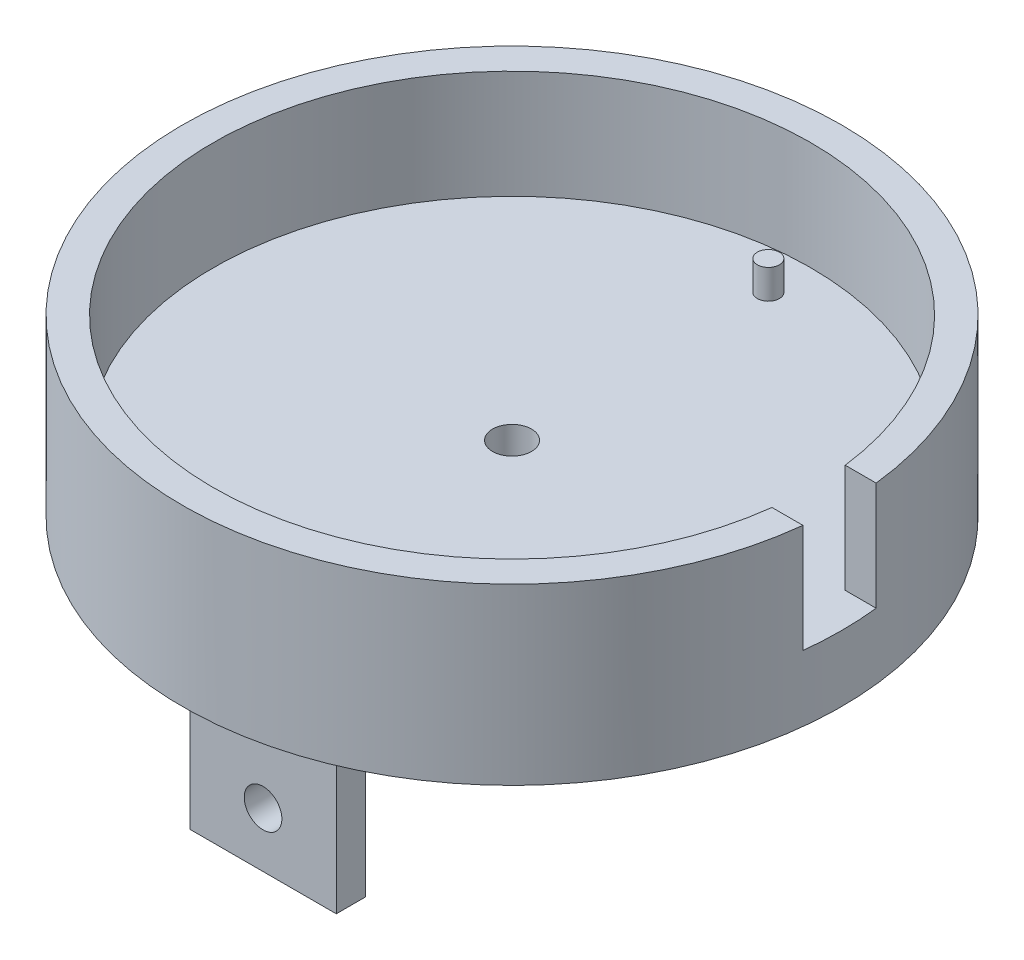
SolidWorks part; units mm, degrees
ref_plane "Front Plane" through (0, 0, 0) normal (0, 0, 1) x (1, 0, 0)
ref_plane "Top Plane" through (0, 0, 0) normal (0, 1, 0) x (1, 0, 0)
ref_plane "Right Plane" through (0, 0, 0) normal (1, 0, 0) x (0, 0, -1)
sketch "Sketch1" plane through (0, 0, 0) normal (0, 0, 1) x (1, 0, 0)
  line L0 (0, 0) -> (0, 120.0887) construction
  line L1 (0, 0) -> (57.15, 0)
  line L2 (57.15, 0) -> (57.15, 30.226)
  line L3 (57.15, 30.226) -> (51.816, 30.226)
  line L4 (51.816, 30.226) -> (51.816, 11.43)
  line L5 (51.816, 11.43) -> (0, 11.43)
  line L6 (0, 11.43) -> (0, 0)
  dimension "D1" = 51.816
  dimension "D2" = 11.43
  dimension "D3" = 5.334
  dimension "D4" = 18.796
revolve "Revolve1" add sketch "Sketch1" angle 360 mid plane about L0
ref_plane "Plane2" through (57.15, 0, 0) normal (1, 0, 0) x (0, 0, -1)
sketch "Sketch4" plane through (57.15, 0, 0) normal (1, 0, 0) x (0, 0, -1)
  line L0 (0, 0) -> (0, 30.226) construction
  line L1 (51.816, 30.226) -> (-51.816, 30.226) construction
  line L3 (51.816, 11.43) -> (-51.816, 11.43) construction
  line L4 (-6.35, 11.43) -> (6.35, 11.43)
  line L5 (-6.35, 11.43) -> (-6.35, 30.226)
  line L6 (-6.35, 30.226) -> (6.35, 30.226)
  line L7 (6.35, 11.43) -> (6.35, 30.226)
  line L8 (57.15, 30.226) -> (-57.15, 30.226) construction
  point P5 (0, 15.113)
  point P14 (0, 11.43)
  dimension "D1" = 12.7
extrude "Cut-Extrude2" cut sketch "Sketch4" against normal up to surface (5.7246 mm away)
sketch "Sketch5" plane through (0, 0, 0) normal (0, -1, 0) x (1, 0, 0)
  circle A0 centre (0, 0) radius 3.3782
  dimension "D1" = 6.7564
extrude "Cut-Extrude3" cut sketch "Sketch5" against normal through all
sketch "Sketch6" plane through (0, 11.43, 0) normal (0, 1, 0) x (1, 0, 0)
  line L0 (51.816, 0) -> (57.15, 0) construction
  line L1 (57.15, -15.5765) -> (57.15, 15.5765) construction
  circle A0 centre (0, 44.45) radius 1.905
  arc A1 (51.4254, 6.35) -> (51.4254, -6.35) centre (0, 0) ccw construction
  circle A2 centre (0, -44.45) radius 1.905
  dimension "D2" = 3.81
  dimension "D1" = 44.45
extrude "Boss-Extrude1" add sketch "Sketch6" along normal blind 5.08
sketch "Sketch7" plane through (0, 0, 0) normal (0, 1, 0) x (1, 0, 0)
  line L0 (-12.7, -38.1) -> (12.7, -43.18) construction
  line L1 (57.15, 0) -> (-57.15, 0) construction
  line L2 (-12.7, -38.1) -> (12.7, -38.1)
  line L3 (-12.7, -38.1) -> (-12.7, -43.18)
  line L4 (-12.7, -43.18) -> (12.7, -43.18)
  line L5 (12.7, -38.1) -> (12.7, -43.18)
  line L6 (-12.7, -43.18) -> (12.7, -38.1) construction
  line L7 (0, -57.15) -> (0, 57.15) construction
  line L8 (-12.7, 38.1) -> (12.7, 38.1)
  line L9 (-12.7, 38.1) -> (-12.7, 43.18)
  line L10 (-12.7, 43.18) -> (12.7, 38.1) construction
  line L11 (-12.7, 38.1) -> (12.7, 43.18) construction
  line L12 (-12.7, 43.18) -> (12.7, 43.18)
  line L14 (12.7, 38.1) -> (12.7, 43.18)
  circle A0 centre (0, 0) radius 57.15 construction
  point P1 (0, -40.64)
  point P6 (0, -40.64)
  point P16 (0, 40.64)
  dimension "D1" = 25.4
  dimension "D2" = 5.08
  dimension "D3" = 40.64
extrude "Boss-Extrude4" add sketch "Sketch7" against normal blind 31.75
fillet "Fillet1" radius 6.35 6 edges at (12.7, 0, -40.64) (0, 0, -43.18) (-12.7, 0, -40.64) (-12.7, 0, 40.64) (12.7, 0, 40.64) (0, 0, 43.18)
sketch "Sketch8" plane through (0, 0, 43.18) normal (0, 0, 1) x (1, 0, 0)
  line L0 (-12.7, -31.75) -> (12.7, -31.75) construction
  line L1 (-12.7, -31.75) -> (-12.7, -6.35) construction
  circle A0 centre (0, -22.225) radius 3.2639
  dimension "D1" = 6.5278
  dimension "D2" = 9.525
  dimension "D3" = 12.7
extrude "Cut-Extrude4" cut sketch "Sketch8" against normal through all both and the other way through all
